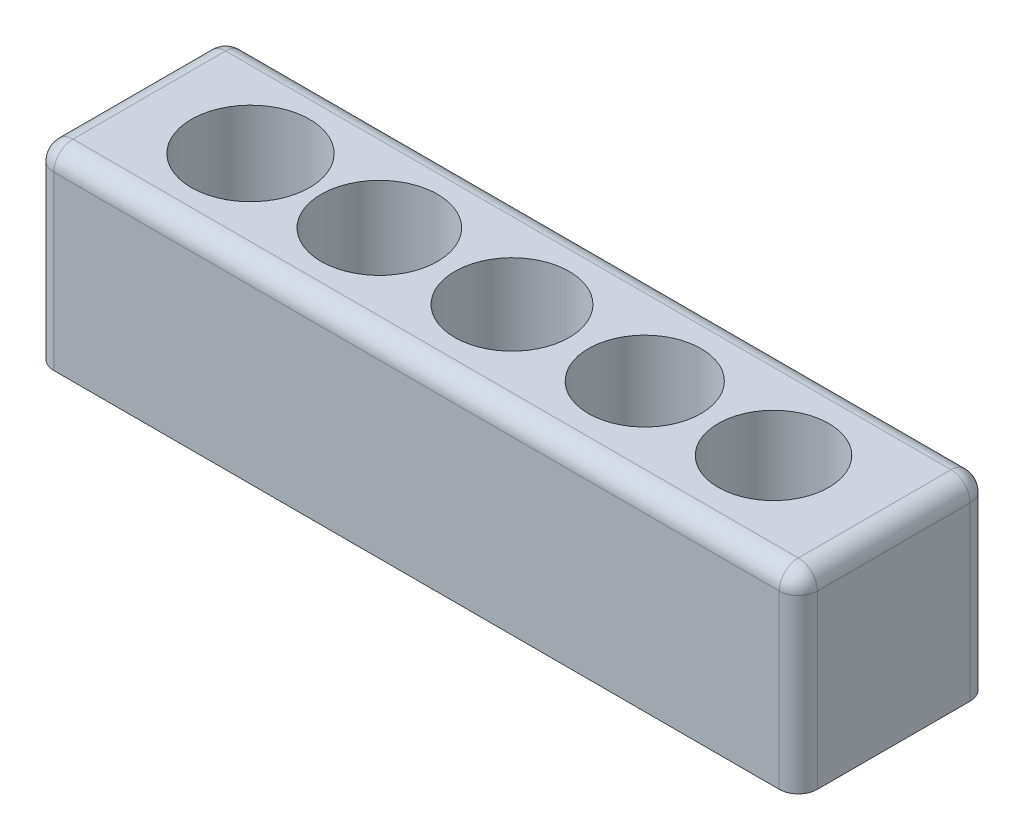
SolidWorks part; units mm, degrees
ref_plane "Front Plane" through (0, 0, 0) normal (0, 0, 1) x (1, 0, 0)
ref_plane "Top Plane" through (0, 0, 0) normal (0, 1, 0) x (1, 0, 0)
ref_plane "Right Plane" through (0, 0, 0) normal (1, 0, 0) x (0, 0, -1)
sketch "Sketch2" plane through (0, 0, 0) normal (0, 1, 0) x (1, 0, 0)
  line L1 (-7.3799, 2.4054) -> (9.6201, 2.4054)
  line L2 (-7.3799, 2.4054) -> (-7.3799, -2.5946)
  line L3 (-7.3799, -2.5946) -> (9.6201, -2.5946)
  line L4 (9.6201, 2.4054) -> (9.6201, -2.5946)
  dimension "D1" = 17
  dimension "D2" = 5
extrude "Boss-Extrude1" add sketch "Sketch2" along normal blind 5
sketch "Sketch3" plane through (0, 5, 0) normal (0, 1, 0) x (1, 0, 0)
  line L0 (-7.3799, -0.0946) -> (9.6201, -0.0946) construction
  line L1 (-7.3799, 2.4054) -> (-7.3799, -2.5946) construction
  line L2 (9.6201, -2.5946) -> (9.6201, 2.4054) construction
  line L3 (1.1201, -0.0946) -> (1.1201, 2.4054) construction
  line L4 (9.6201, 2.4054) -> (-7.3799, 2.4054) construction
  line L5 (1.1201, 2.4054) -> (1.1201, -2.5946) construction
  line L6 (-7.3799, -2.5946) -> (9.6201, -2.5946) construction
  circle A0 centre (1.1201, -0.0946) radius 1.5
  circle A1 centre (7.9701, -0.0946) radius 1.45
  circle A2 centre (-5.7299, -0.0946) radius 1.55
  circle A3 centre (-2.3545, -0.0946) radius 1.525
  circle A4 centre (4.5971, -0.0946) radius 1.475
  dimension "D1" = 3
  dimension "D2" = 2.9
  dimension "D3" = 1.65
  dimension "D4" = 3.1
  dimension "D5" = 1.65
  dimension "D6" = 3.05
  dimension "D7" = 2.95
extrude "Cut-Extrude1" cut sketch "Sketch3" against normal through all
sketch "Sketch4" plane through (-7.3799, 0, 0) normal (-1, 0, 0) x (0, 0, 1)
  line L1 (-2.4054, 5) -> (2.5946, 5)
  line L2 (-2.4054, 5) -> (-2.4054, 0)
  line L3 (-2.4054, 0) -> (2.5946, 0)
  line L4 (2.5946, 5) -> (2.5946, 0)
extrude "Boss-Extrude2" add sketch "Sketch4" along normal blind 1.5
sketch "Sketch5" plane through (9.6201, 0, 0) normal (1, 0, 0) x (0, 0, -1)
  line L1 (-2.5946, 5) -> (2.4054, 5)
  line L2 (-2.5946, 5) -> (-2.5946, 0)
  line L3 (-2.5946, 0) -> (2.4054, 0)
  line L4 (2.4054, 5) -> (2.4054, 0)
extrude "Boss-Extrude3" add sketch "Sketch5" along normal blind 1.5
fillet "Fillet1" radius 0.5 8 edges at (-8.8799, 2.5, 2.5946) (1.1201, 5, 2.5946) (11.1201, 2.5, 2.5946) (11.1201, 5, 0.0946) (11.1201, 2.5, -2.4054) (1.1201, 5, -2.4054) (-8.8799, 5, 0.0946) (-8.8799, 2.5, -2.4054)
